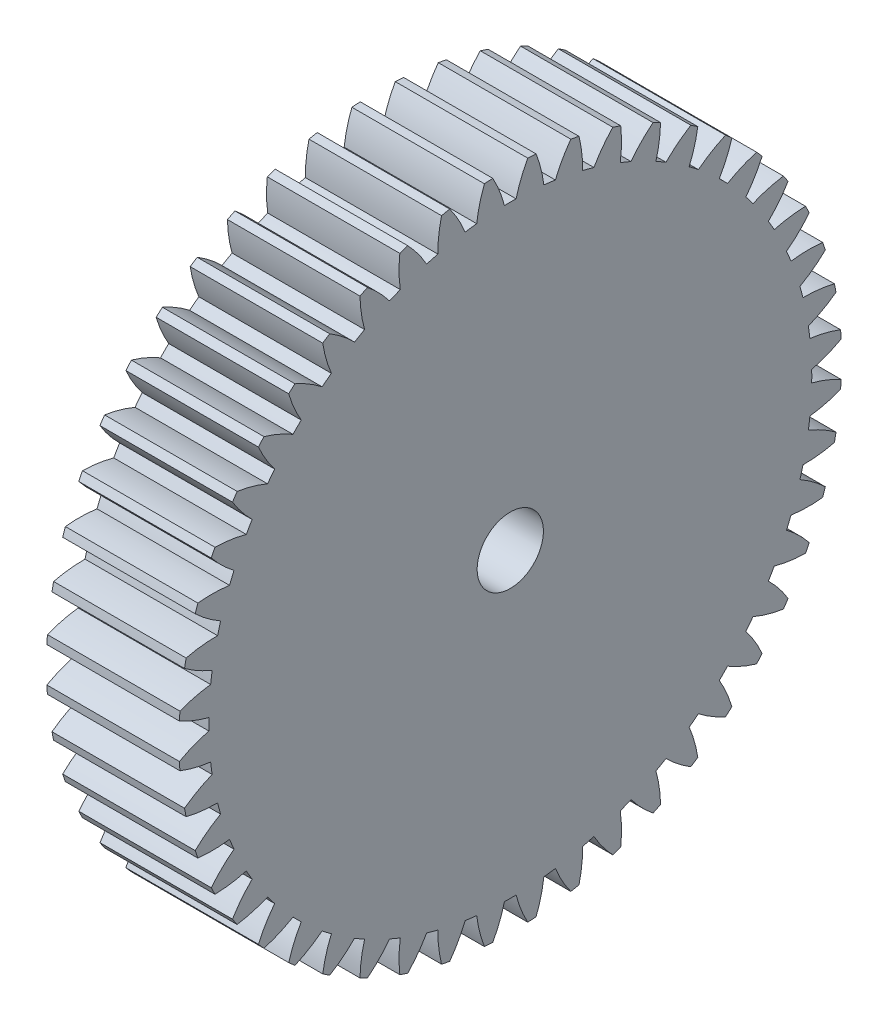
SolidWorks part; units mm, degrees
ref_plane "Plane1" through (0, 0, 0) normal (0, 0, 1) x (1, 0, 0)
ref_plane "Plane2" through (0, 0, 0) normal (0, 1, 0) x (1, 0, 0)
ref_plane "Plane3" through (0, 0, 0) normal (1, 0, 0) x (0, 0, -1)
other "Configuration Table"
sketch "HoldingSke" plane through (0, 0, 0) normal (0, 1, 0) x (1, 0, 0)
  line L0 (0, 0) -> (0.6691, -0.7431)
  line L1 (-15, 0) -> (100, 0) construction
  line L2 (0, 0) -> (-2.1039, 2.3779)
  line L3 (0, 0) -> (-11.863, 4.5341)
  line L4 (0, 0) -> (5.7786, 6.4178)
  line L5 (0, 0) -> (-46.8476, -17.4728)
  line L6 (0, 0) -> (-8.2896, -5.593)
  line L7 (-2.1039, 2.3779) -> (8.6586, 51.2059)
  line L8 (-76.2, 54.61) -> (-75.3, 54.61)
  line L9 (-71.009, 38.7566) -> (-53.1078, 45.2721)
  line L10 (-76.2, 71.12) -> (104.1128, 71.12)
  line L11 (0, 0) -> (-10, 0)
  line L12 (-76.2, 101.6) -> (-76.162, 101.6)
  line L13 (24.9733, 27.94) -> (52.9518, 28.4284)
  line L14 (24.9733, 27.94) -> (24.9743, 27.94)
  line L15 (24.9733, 27.94) -> (100.4006, 29.5858)
  line L16 (-63.627, -1) -> (-12.827, -1)
  circle A0 centre (0, 0) radius 2.5
  circle A1 centre (0, 0) radius 22.749
  circle A2 centre (0, 0) radius 37.5
  circle A3 centre (0, 0) radius 2.5
  dimension "MHD" = 45.498
  dimension "Hub_dia" = 75
  dimension "Bore" = 5
  dimension "MBD" = 5
  dimension "Num_teeth" = 48
  dimension "Pitch" = 1
  dimension "Overall_len" = 50
  dimension "Show_teeth" = 48
  dimension "Thickness" = 10
  dimension "OAL" = 50.0001
  dimension "T_dim" = 0.9
  dimension "Ap" = 20
  dimension "H" = 19.05
  dimension "Pitch_radius" = 180.3128
  dimension "Width" = 10
  dimension "Backlash" = 0.038
  dimension "Addendum_fac" = 1
  dimension "Dedendum_fac" = 1.25
  dimension "Clearance_fac" = 0.25
  dimension "Dedendum_add" = 0.001
  dimension "Module" = 1
sketch "BasProSke" plane through (0, 0, 0) normal (0, 1, 0) x (1, 0, 0)
  line L0 (-10, 0) -> (60, 0) construction
  line L1 (0, 0) -> (0, 25)
  line L2 (0, 0) -> (10, 0)
  line L3 (10, 0) -> (10, 25)
  line L4 (10, 25) -> (0, 25)
  dimension "Thickness" = 10
  dimension "Diameter" = 50
revolve "Base-Revolve" add sketch "BasProSke" angle 360 about L0
sketch "TooCutSke" plane through (0, 0, 0) normal (1, 0, 0) x (0, 0, -1)
  line L1 (0, 0) -> (0, 107) construction
  line L2 (0, 0) -> (-0.8518, 23.9849) construction
  line L3 (0, 0) -> (-3.1379, 47.8757) construction
  line L4 (-0.8518, 23.9849) -> (-1.569, 23.9379) construction
  arc A0 (0.4395, 22.7448) -> (-0.4395, 22.7448) centre (0, 0) ccw
  arc A1 (1.3336, 24.9898) -> (-1.3336, 24.9898) centre (0, 0) ccw
  circle A2 centre (0, 0) radius 24 construction
  circle A3 centre (0, 0) radius 22.5526 construction
  arc A4 (-0.4395, 22.7448) -> (-1.3336, 24.9898) centre (-9.7344, 20.3436) ccw
  arc A5 (1.3336, 24.9898) -> (0.4395, 22.7448) centre (9.7344, 20.3436) ccw
  dimension "Root_dia" = 45.498
  dimension "Overcut_dia" = 50.0508
  dimension "Pitch_dia" = 48
  dimension "Base_dia" = 45.1052
  dimension "Flank_rad" = 9.6
  dimension "Half_ang" = 3.75
  dimension "Half_CT" = 0.7188
extrude "ToothCut" cut sketch "TooCutSke" along normal through all
fillet "Breaks" [suppressed] radius 0.02
fillet "RootFillets" [suppressed] radius 0.251
pattern_circular "TeethCuts" count 48 every 7.5 about axis through (-10, 0, 0) along (1, 0, 0) of "ToothCut", "RootFillets", "Breaks"
sketch "HubNeaOneSke" plane through (0, 0, 0) normal (-1, 0, 0) x (0, 0, 1)
  circle A0 centre (0, 0) radius 22.749
  dimension "Diameter" = 45.498
extrude "HubNearOne" [suppressed] add sketch "HubNeaOneSke" along normal blind 40.0001
sketch "HubNeaBotSke" plane through (0, 0, 0) normal (-1, 0, 0) x (0, 0, 1)
  circle A0 centre (0, 0) radius 22.749
  dimension "Diameter" = 45.498
extrude "HubNearBoth" [suppressed] add sketch "HubNeaBotSke" along normal blind 20
ref_plane "FarPln" through (10, 0, 0) normal (1, 0, 0) x (0, 0, -1)
sketch "HubFarSke" plane through (10, 0, 0) normal (1, 0, 0) x (0, 0, -1)
  circle A0 centre (0, 0) radius 22.749
  dimension "Diameter" = 45.498
extrude "HubFar" [suppressed] add sketch "HubFarSke" along normal blind 20
sketch "BorSke" plane through (0, 0, 0) normal (1, 0, 0) x (0, 0, -1)
  circle A0 centre (0, 0) radius 2.5
  dimension "Diameter" = 5
extrude "Bore" cut sketch "BorSke" along normal mid plane 100.0001
sketch "KeySke" plane through (0, 0, 0) normal (1, 0, 0) x (0, 0, -1)
  line L0 (-1, 0) -> (-1, 3.4)
  line L1 (-1, 3.4) -> (1, 3.4)
  line L2 (1, 3.4) -> (1, 0)
  line L3 (0, 0) -> (0, 34) construction
  line L4 (-1, 0) -> (1, 0)
  dimension "Offset" = 3.4
  dimension "Width" = 2
extrude "Keyway" [suppressed] cut sketch "KeySke" along normal mid plane 100.0001
pattern_circular "Keyway2" [suppressed] count 2 every 90 about axis through (-10, 0, 0) along (1, 0, 0)
equation "' \"Module@HoldingSke\" = 6.35"
equation "' \"Num_teeth@HoldingSke\" = 12"
equation "' \"Ap@HoldingSke\" =  20"
equation "' \"Ap@HoldingSke\" = 20"
equation "' \"Width@HoldingSke\" = 0.5 * 25.4"
equation "' \"Hub_dia@HoldingSke\"= 1 * 25.4"
equation "' \"Hub_dia@HoldingSke\" = 1 * 25.4"
equation "' \"Overall_len@HoldingSke\" = 1.0 * 25.4"
equation "' \"Bore@HoldingSke\" = 0.75 * 25.4"
equation "' \"T_dim@HoldingSke\" = 0.1 * 25.4"
equation "' \"Width@KeySke\" = 0.25 * 25.4"
equation "' \"Show_teeth@HoldingSke\" = 13"
equation "' \"Backlash@HoldingSke\" = 0.009 * 25.4"
equation "' \"Addendum_fac@HoldingSke\" = 1.0"
equation "' \"Dedendum_fac@HoldingSke\" = 1.25"
equation "' \"Dedendum_add@HoldingSke\" = 0.00005 * 25.4"
equation "' \"Clearance_fac@HoldingSke\" = 0.25"
equation "\"Pitch@HoldingSke\" = 1 / \"Module@HoldingSke\""
equation "\"Overcut_dia@TooCutSke\" = (\"Num_teeth@HoldingSke\" + 2 * \"Addendum_fac@HoldingSke\") / \"Pitch@HoldingSke\" + 0.002 * 25.4"
equation "\"Pitch_dia@TooCutSke\" = \"Num_teeth@HoldingSke\" / \"Pitch@HoldingSke\""
equation "\"Base_dia@TooCutSke\" = \"Num_teeth@HoldingSke\" / \"Pitch@HoldingSke\" * cos((\"Ap@HoldingSke\"  * 3.14159265 / 180))"
equation "\"Root_dia@TooCutSke\" = (\"Num_teeth@HoldingSke\" + 2) / \"Pitch@HoldingSke\" - 2 * (\"Addendum_fac@HoldingSke\" + \"Dedendum_fac@HoldingSke\") / \"Pitch@HoldingSke\" - \"Dedendum_add@HoldingSke\" * 2"
equation "\"Half_ang@TooCutSke\" = 180 / \"Num_teeth@HoldingSke\""
equation "\"Half_CT@TooCutSke\" = \"Num_teeth@HoldingSke\" / \"Pitch@HoldingSke\" * sin((3.14159265 / 2 / \"Num_teeth@HoldingSke\")) / 2 - 7 * \"Backlash@HoldingSke\" / 4"
equation "\"Flank_rad@TooCutSke\" = \"Num_teeth@HoldingSke\" / \"Pitch@HoldingSke\" / 5"
equation "\"Radius@RootFillets\" = \"Clearance_fac@HoldingSke\" / \"Pitch@HoldingSke\" + \"Dedendum_add@HoldingSke\""
equation "\"Break_rad@Breaks\" = 0.02 / \"Pitch@HoldingSke\""
equation "\"Thickness@HoldingSke\" = \"Width@HoldingSke\""
equation "\"OAL@HoldingSke\" = \"Thickness@HoldingSke\""
equation "\"MHD@HoldingSke\" = (\"Num_teeth@HoldingSke\" + 2) / \"Pitch@HoldingSke\" - 2 * (\"Addendum_fac@HoldingSke\" + \"Dedendum_fac@HoldingSke\")  / \"Pitch@HoldingSke\" - \"Dedendum_add@HoldingSke\" * 2"
equation "\"MBD@HoldingSke\" = (\"Num_teeth@HoldingSke\" + 2) / \"Pitch@HoldingSke\" - 2 * (\"Addendum_fac@HoldingSke\" + \"Dedendum_fac@HoldingSke\")  / \"Pitch@HoldingSke\" - \"Dedendum_add@HoldingSke\" * 2 - 0.002 * 25.4"
equation "\"MHD@HoldingSke\" = ((sgn( \"MHD@HoldingSke\" - \"Hub_dia@HoldingSke\" )-1)*( \"MHD@HoldingSke\" - \"Hub_dia@HoldingSke\" ))/-2+ \"Hub_dia@HoldingSke\""
equation "\"MBD@HoldingSke\" = ((sgn( \"MBD@HoldingSke\" - \"Bore@HoldingSke\" )-1)*( \"MBD@HoldingSke\" - \"Bore@HoldingSke\" ))/-2+ \"Bore@HoldingSke\""
equation "\"OAL@HoldingSke\" = ((sgn( \"OAL@HoldingSke\" - \"Overall_len@HoldingSke\" )+1)*( \"OAL@HoldingSke\" - \"Overall_len@HoldingSke\" ))/2 + \"Overall_len@HoldingSke\" + 0.000002 * 25.4"
equation "\"Num_teeth@TeethCuts\" = int( \"Show_teeth@HoldingSke\" ) + 1"
equation "\"Num_teeth@TeethCuts\" = ((sgn( \"Num_teeth@TeethCuts\" - \"Num_teeth@HoldingSke\" )-1)*( \"Num_teeth@TeethCuts\" - \"Num_teeth@HoldingSke\" ))/-2+ \"Num_teeth@HoldingSke\""
equation "\"Num_teeth@TeethCuts\" = ((sgn( \"Num_teeth@TeethCuts\" - 2.0)+1)*( \"Num_teeth@TeethCuts\" - 2.0))/2 +2.0"
equation "\"Angle@TeethCuts\" = 360.0 / \"Num_teeth@HoldingSke\""
equation "\"Diameter@BasProSke\" = (\"Num_teeth@HoldingSke\" + 2 * \"Addendum_fac@HoldingSke\") / \"Pitch@HoldingSke\""
equation "\"Thickness@BasProSke\"  = \"Thickness@HoldingSke\""
equation "' \"Fillet_rad@BasProSke\" =  \"Thickness@HoldingSke\" * 0.05"
equation "' \"Fillet_rad@BasProSke\" = \"Thickness@HoldingSke\" * 0.05"
equation "\"MHD@HoldingSke\" = ((sgn( \"MHD@HoldingSke\" - \"Root_dia@TooCutSke\" )-1)*( \"MHD@HoldingSke\" - \"Root_dia@TooCutSke\" ))/-2+ \"Root_dia@TooCutSke\""
equation "\"Diameter@HubNeaOneSke\" = \"MHD@HoldingSke\""
equation "\"Length@HubNearOne\" = \"OAL@HoldingSke\" - \"Thickness@BasProSke\""
equation "\"Diameter@HubNeaBotSke\" = \"MHD@HoldingSke\""
equation "\"Length@HubNearBoth\" = ( \"OAL@HoldingSke\" - \"Thickness@BasProSke\" ) / 2.0"
equation "\"Thickness@FarPln\" = \"Thickness@BasProSke\""
equation "\"Diameter@HubFarSke\" = \"MHD@HoldingSke\""
equation "\"Length@HubFar\" = ( \"OAL@HoldingSke\" - \"Thickness@BasProSke\" ) / 2.0"
equation "\"Diameter@BorSke\" = \"MBD@HoldingSke\""
equation "\"D1@Bore\" = \"OAL@HoldingSke\" * 2.0"
equation "\"D1@Keyway\" = \"OAL@HoldingSke\" * 2.0"
equation "\"Offset@KeySke\" = \"T_dim@HoldingSke\" + \"MBD@HoldingSke\" / 2.0"
